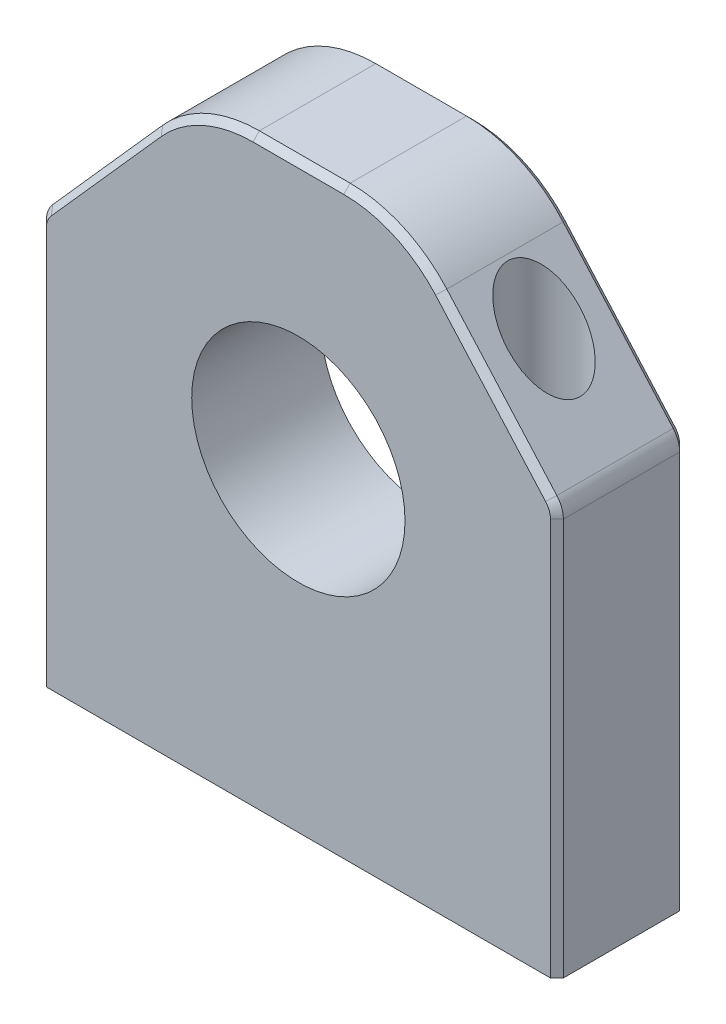
SolidWorks part; units mm, degrees
ref_plane "Front Plane" through (0, 0, 0) normal (0, 0, 1) x (1, 0, 0)
ref_plane "Top Plane" through (0, 0, 0) normal (0, 1, 0) x (1, 0, 0)
ref_plane "Right Plane" through (0, 0, 0) normal (1, 0, 0) x (0, 0, -1)
sketch "Sketch1" plane through (0, 0, 0) normal (0, 0, 1) x (1, 0, 0)
  line L0 (8, 45) -> (-8, 45)
  line L1 (-8, 45) -> (-20, 31.5)
  line L2 (-20, 31.5) -> (-20, 0)
  line L3 (-20, 0) -> (20, 0)
  line L4 (0, 0) -> (0, 45) construction
  line L5 (20, 31.5) -> (20, 0)
  line L6 (8, 45) -> (20, 31.5)
  circle A0 centre (0, 25) radius 8.25
  dimension "D6" = 16.5
  dimension "D1" = 20
  dimension "D2" = 45
  dimension "D3" = 31.5
  dimension "D4" = 8
  dimension "D5" = 25
extrude "Boss-Extrude1" add sketch "Sketch1" along normal blind 10 contours L4 L3 L5 L6 L0 | L3 L4 L0 L1 L2
sketch "Sketch2" plane through (0, 45, 0) normal (0, 1, 0) x (1, 0, 0)
  line L0 (20, 0) -> (8, 0) construction
  line L1 (8, 0) -> (8, -10) construction
  line L2 (8, -10) -> (20, -10) construction
  line L3 (20, -10) -> (20, 0) construction
  line L4 (-8, 0) -> (-20, 0) construction
  line L5 (-20, 0) -> (-20, -10) construction
  line L6 (-20, -10) -> (-8, -10) construction
  line L7 (-8, -10) -> (-8, 0) construction
  line L8 (20, 0) -> (8, 0)
  line L9 (8, 0) -> (8, -10)
  line L10 (8, -10) -> (20, -10)
  line L11 (20, -10) -> (20, 0)
  line L12 (-8, 0) -> (-20, 0)
  line L13 (-20, 0) -> (-20, -10)
  line L14 (-20, -10) -> (-8, -10)
  line L15 (-8, -10) -> (-8, 0)
  circle A0 centre (-14, -5) radius 2.8
  circle A1 centre (14, -5) radius 2.8
  point P2 (-14, -5)
  point P4 (14, -5)
  point P17 (-20, -5)
  dimension "D1" = 5.6
  dimension "D2" = 6
  dimension "D3" = 6
hole_wizard "M3 Clearance Hole1" positions "3DSketch1" profile "Sketch4" hole size "M3" standard "ISO"
sketch3d "3DSketch1"
  point P0 (-14, 45, 5)
  point P3 (14, 45, 5)
sketch "Sketch4" plane through (-14, 45, 5) normal (1, 0, 0) x (0, 0, 1)
  line L0 (0, 0) -> (0, 46.0205)
  line L1 (0, 46.0205) -> (1.7, 44.999)
  line L2 (1.7, 44.999) -> (1.7, 0)
  line L5 (1.7, 0) -> (0, 0)
  line L10 (0, 46.0205) -> (-1.7, 44.999) construction
  line L11 (0, -6.35) -> (0, 107.95) construction
  dimension "Hole Dia." = 3.4
  dimension "Hole Depth" = 44.999
  dimension "Drill Angle" = 118
extrude "Cut-Extrude1" cut sketch "Sketch2" against normal offset from surface (35 mm away) 10 contours A1 | A0 up to face at (0, 0, 5)
fillet "Fillet1" radius 10 2 edges at (-8, 45, 5) (8, 45, 5)
fillet "Fillet2" radius 2 2 edges at (-20, 31.5, 5) (20, 31.5, 5)
chamfer "Chamfer1" distance 0.5 angle 45 18 edges at (-20, 15.3698, 10) (-19.8694, 31.4504, 10) (-15.2391, 36.856, 10) (-7.6059, 44.1224, 10) (0, 45, 10) (20, 15.3698, 10) (7.6059, 44.1224, 10) (19.8694, 31.4504, 10) (15.2391, 36.856, 10) (-20, 15.3698, 0) (-19.8694, 31.4504, 0) (-15.2391, 36.856, 0) (20, 15.3698, 0) (-7.6059, 44.1224, 0) (19.8694, 31.4504, 0) (0, 45, 0) (15.2391, 36.856, 0) (7.6059, 44.1224, 0)
equation "\"B\"= 16mm'bearing OD"
equation "\"To\"= 0.5mm'Tolerance"
equation "\"D6@Sketch1\"=\"B\"+\"To\""
equation "\"H\"= 45mm'Height"
equation "\"D2@Sketch1\"=\"H\""
equation "\"D3@Sketch1\"=\"H\"*0.7"
equation "\"D5@Sketch1\"=\"HH\""
equation "\"W\"= 20mm'width"
equation "\"D1@Sketch1\"=\"W\""
equation "\"D4@Sketch1\"=\"W\"*0.4"
equation "\"T\"= 10mm'thickness"
equation "\"D1@Boss-Extrude1\"=\"T\""
equation "\"HH\"= 25mm'hole height"
